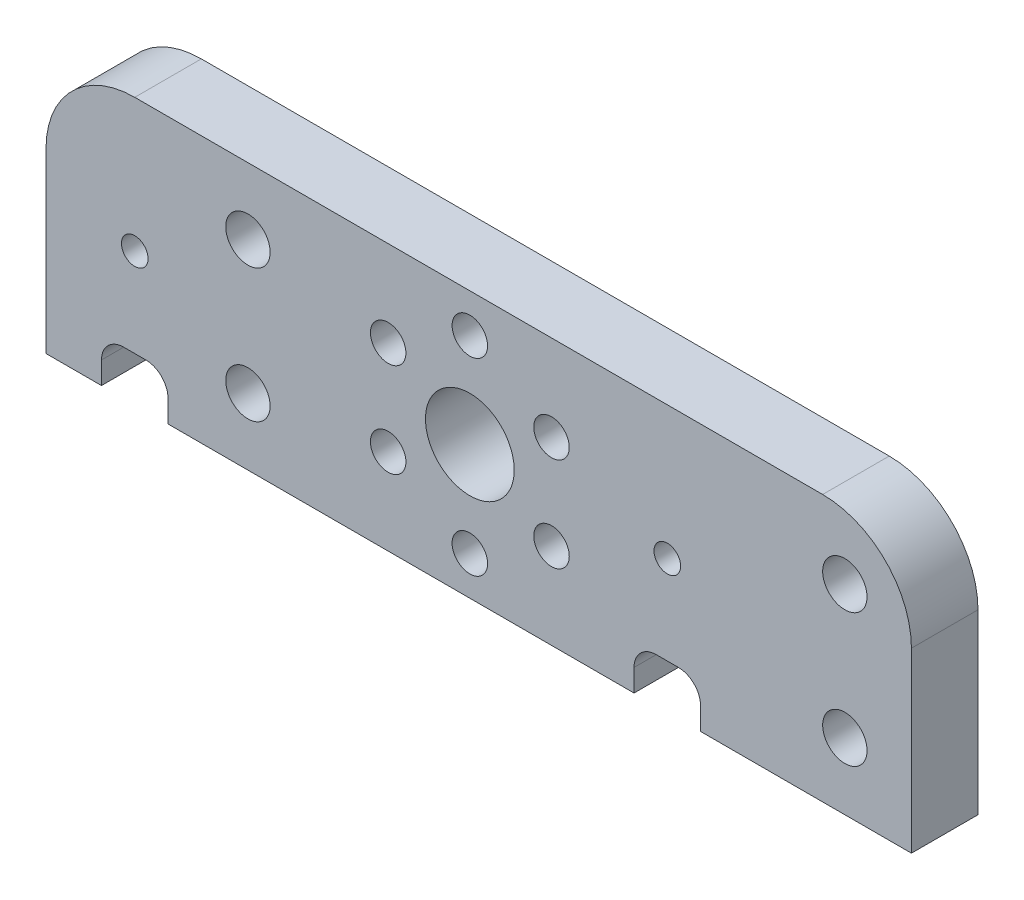
SolidWorks part; units mm, degrees
ref_plane "Front Plane" through (0, 0, 0) normal (0, 0, 1) x (1, 0, 0)
ref_plane "Top Plane" through (0, 0, 0) normal (0, 1, 0) x (1, 0, 0)
ref_plane "Right Plane" through (0, 0, 0) normal (1, 0, 0) x (0, 0, -1)
sketch "Sketch1" plane through (0, 0, 0) normal (0, 0, 1) x (1, 0, 0)
  line L0 (-23.1, 0) -> (15.9, 0) construction
  line L1 (-23.1, -6) -> (15.9, -6)
  line L2 (-23.1, -6) -> (-23.1, 2)
  line L3 (-19.1, 6) -> (11.9, 6)
  line L4 (15.9, -6) -> (15.9, 2)
  line L5 (12.9, -6) -> (12.9, 6.9573) construction
  line L6 (-14, -6) -> (-14, 8.3224) construction
  line L7 (-23.1, -3) -> (15.9, -3) construction
  line L8 (-22.973, 3) -> (15.773, 3) construction
  line L11 (3.4, -6) -> (3.4, -5)
  line L12 (4.4, -4) -> (5.4, -4)
  line L13 (6.4, -6) -> (6.4, -5)
  line L14 (4.9, -6) -> (6.4, -4) construction
  line L15 (3.4, -4) -> (4.9, -6) construction
  line L17 (-20.6, -6) -> (-20.6, -5)
  line L18 (-19.6, -4) -> (-18.6, -4)
  line L19 (-17.6, -6) -> (-17.6, -5)
  line L20 (-19.1, -6) -> (-17.6, -4) construction
  line L21 (-20.6, -4) -> (-19.1, -6) construction
  circle A0 centre (-4, 0) radius 2
  circle A1 centre (4.9, 0) radius 0.6
  arc A2 (11.9, 6) -> (15.9, 2) centre (11.9, 2) cw
  arc A3 (-23.1, 2) -> (-19.1, 6) centre (-19.1, 2) cw
  circle A4 centre (-19.1, 0) radius 0.6
  circle A5 centre (12.9, 3) radius 1
  circle A6 centre (12.9, -3) radius 1
  circle A7 centre (-14, -3) radius 1
  circle A8 centre (-14, 3) radius 1
  arc A9 (5.4, -4) -> (6.4, -5) centre (5.4, -5) cw
  arc A10 (3.4, -5) -> (4.4, -4) centre (4.4, -5) cw
  arc A11 (-18.6, -4) -> (-17.6, -5) centre (-18.6, -5) cw
  arc A12 (-20.6, -5) -> (-19.6, -4) centre (-19.6, -5) cw
  point P0 (0, 0)
  point P34 (4.9, -6)
  point P36 (-19.1, -4)
  point P39 (-19.1, -6)
  point P49 (4.9, -4)
  dimension "D1" = 8.9
  dimension "D2" = 1.2
  dimension "D3" = 4
  dimension "D6" = 4
  dimension "D7" = 4
  dimension "D8" = 11
  dimension "D4" = 24
  dimension "D5" = 4
  dimension "D11" = 1.2
  dimension "D16" = 2
  dimension "D17" = 2
  dimension "D18" = 2
  dimension "D19" = 2
  dimension "D23" = 1
  dimension "D9" = 12
  dimension "D10" = 6
  dimension "D12" = 10
  dimension "D13" = 3
  dimension "D14" = 3
  dimension "D15" = 3
  dimension "D20" = 3
  dimension "D21" = 2
  dimension "D22" = 3
extrude "Boss-Extrude1" add sketch "Sketch1" along normal blind 3 contours L17 A12 L18 A11 L19 L1 L11 A10 L12 A9 L13 L4 A2 L3 A3 L2 A8 A7 A6 A5 A4 A1 A0
sketch "Sketch2" plane through (0, 0, 0) normal (0, 0, 1) x (1, 0, 0)
  circle A0 centre (4.9, 0) radius 0.75
  circle A1 centre (4.9, 0) radius 2.75
  dimension "D1" = 2
extrude "Boss-Extrude2" [suppressed] add sketch "Sketch2" along normal blind 1
sketch "Sketch3" plane through (0, 0, 3) normal (0, 0, 1) x (1, 0, 0)
  circle A0 centre (-4, 0) radius 4.25
  circle A1 centre (-4, 4.25) radius 0.8
  dimension "D1" = 8.5
  dimension "D2" = 1.6
extrude "Cut-Extrude1" cut sketch "Sketch3" against normal blind 3 contours A0 A1 | A0 A1
pattern_circular "CirPattern1" count 6 over 360 about axis through (-4, 0, 0) along (0, 0, 1) of "Cut-Extrude1"
